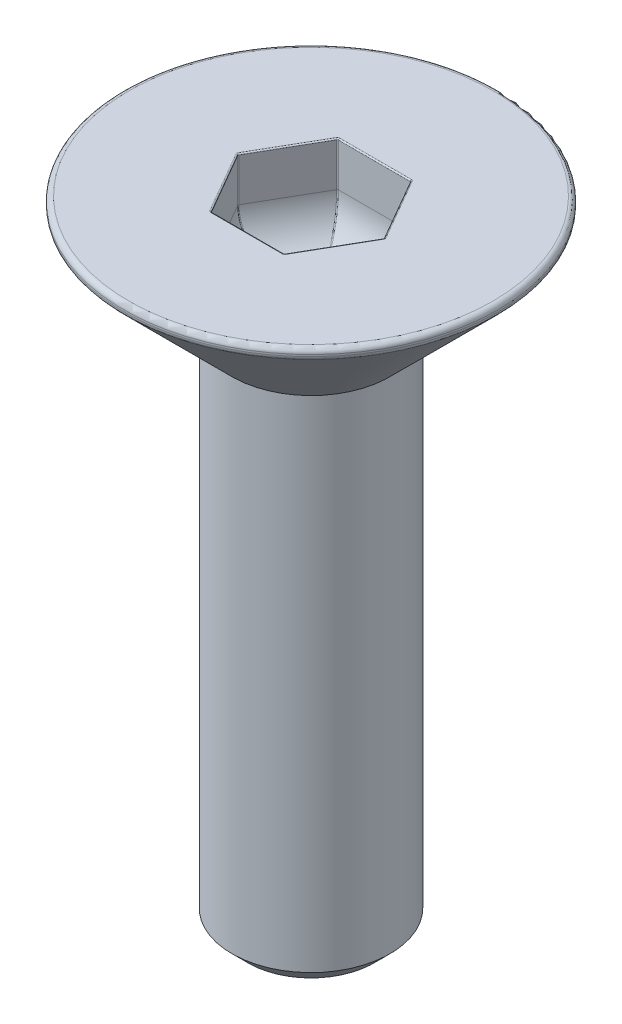
SolidWorks part; units mm, degrees
ref_plane "Front" through (0, 0, 0) normal (0, 0, 1) x (1, 0, 0)
ref_plane "Top" through (0, 0, 0) normal (0, 1, 0) x (1, 0, 0)
ref_plane "Right" through (0, 0, 0) normal (1, 0, 0) x (0, 0, -1)
sketch "Sketch8" plane through (0, 0, 0) normal (0, 0, 1) x (1, 0, 0)
  line L1 (0, 0) -> (1.25, 0)
  line L2 (0, 0) -> (0, -10)
  line L3 (0, -10) -> (1.25, -10)
  line L4 (1.25, 0) -> (1.25, -10)
  dimension "D1" = 10
revolve "Revolve1" add sketch "Sketch8" angle 360 about L2
chamfer "Chamfer1" distance 0.25 angle 45 1 edges at (-1.25, -10, 0)
sketch "Sketch9" plane through (0, 0, 0) normal (0, 1, 0) x (1, 0, 0)
  circle A0 centre (0, 0) radius 1.5
thread "Thread2" pitch 0.5 start angle 0, offset 0, length 15, pitch 0.5, diameter 3
ref_plane "Plane2" through (-1.5, 0, 0) normal (0, 0, -1) x (1, 0, 0)
sketch "Thread Profile2" plane through (-1.5, 0, 0) normal (0, 0, -1) x (1, 0, 0)
  line L0 (0, 0) -> (0, 0.5) construction
  line L11 (0, 0.4375) -> (0, 0)
  line L12 (0, 0) -> (0.2706, 0.1563)
  line L13 (0.2706, 0.1563) -> (0.2706, 0.2813)
  line L15 (0.2706, 0.2813) -> (0, 0.4375)
  line L17 (0.2706, 0.2188) -> (0, 0.2188) construction
  point P3 (0, 0)
  dimension "Pitch" = 0.5
  dimension "Profile_Angle" = 60
  dimension "Profile_Land" = 0.125
  dimension "Profile_Height" = 0.2706
sketch "Sketch13" plane through (0, 0, 0) normal (0, 0, 1) x (1, 0, 0)
  line L0 (0, 0) -> (3.1, 0)
  line L1 (0, 0) -> (0, -3.1)
  line L2 (0, -3.1) -> (3.1, 0)
  line L3 (1.55, 0) -> (1.55, -1.55) construction
revolve "Revolve2" add sketch "Sketch13" angle 360 about L1
chamfer "Chamfer2" distance 0.2 angle 45 1 edges at (-3.1, 0, 0)
fillet "Fillet1" radius 0.08 2 edges at (2.9586, 0, 0) (2.9586, -0.1414, 0)
sketch "Sketch14" plane through (0, 0, 0) normal (0, 1, 0) x (1, 0, 0)
  line L1 (1.1547, 0) -> (0.5774, 1)
  line L2 (0.5774, 1) -> (-0.5774, 1)
  line L3 (-0.5774, 1) -> (-1.1547, 0)
  line L4 (-1.1547, 0) -> (-0.5774, -1)
  line L5 (-0.5774, -1) -> (0.5774, -1)
  line L6 (0.5774, -1) -> (1.1547, 0)
  circle A0 centre (0, 0) radius 1 construction
extrude "Cut-Extrude1" cut sketch "Sketch14" against normal blind 1.5
fillet "Fillet2" radius 0.8 6 edges at (0, -1.5, 1) (-0.866, -1.5, 0.5) (-0.866, -1.5, -0.5) (0, -1.5, -1) (0.866, -1.5, -0.5) (0.866, -1.5, 0.5)
fillet "Fillet5" radius 0.02 18 edges at (0, 0, -1) (-0.866, 0, -0.5) (-0.866, 0, 0.5) (0, 0, 1) (0.866, 0, 0.5) (0.866, 0, -0.5) (-0.8841, -1.2657, 0) (-0.4421, -1.2657, 0.7657) (0.4421, -1.2657, 0.7657) (0.8841, -1.2657, 0) (0.4421, -1.2657, -0.7657) (-0.4421, -1.2657, -0.7657) (-1.1547, -0.35, 0) (-0.5774, -0.35, 1) (0.5774, -0.35, 1) (1.1547, -0.35, 0) (0.5774, -0.35, -1) (-0.5774, -0.35, -1)
equation "\"length\"= 10"
equation "\"D1@Sketch8\"=\"length\""
